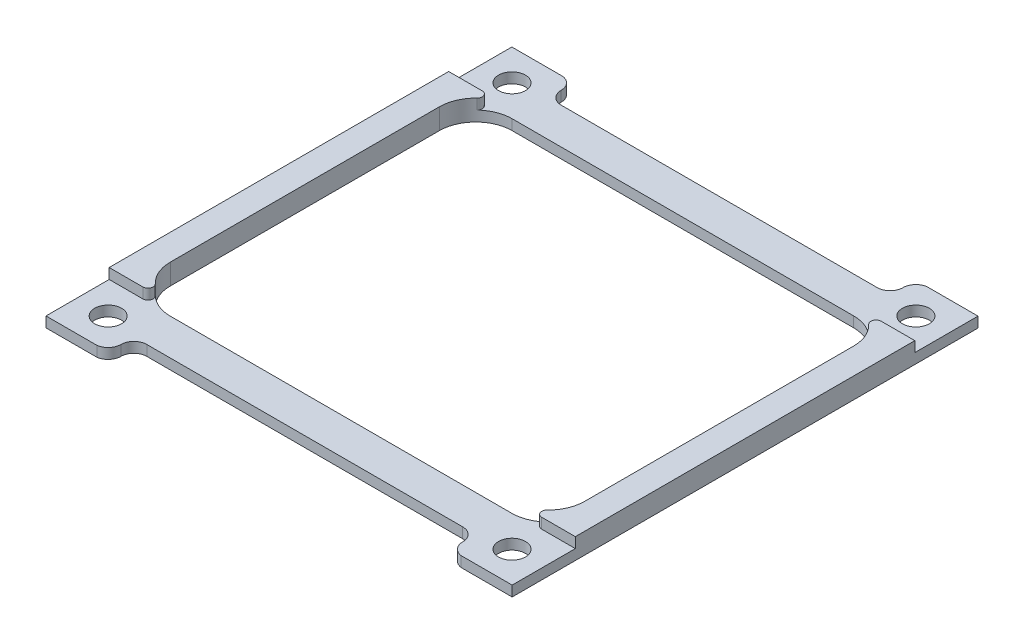
SolidWorks part; units mm, degrees
ref_plane "前视基准面" through (0, 0, 0) normal (0, 0, 1) x (1, 0, 0)
ref_plane "上视基准面" through (0, 0, 0) normal (0, 1, 0) x (1, 0, 0)
ref_plane "右视基准面" through (0, 0, 0) normal (1, 0, 0) x (0, 0, -1)
other "Configuration Table"
sketch "草图1" plane through (0, 0, 0) normal (0, 1, 0) x (1, 0, 0)
  line L1 (-39, 39) -> (39, 39) construction
  line L2 (-39, 39) -> (-39, -39) construction
  line L3 (-39, -39) -> (39, -39) construction
  line L4 (39, 39) -> (39, -39) construction
  line L9 (-45.0151, 44.9851) -> (45.0151, 44.9851)
  line L10 (-45.0151, 44.9851) -> (-45.0151, -44.9851)
  line L15 (-45.0151, -44.9851) -> (45.0151, -44.9851)
  line L16 (45.0151, 44.9851) -> (45.0151, -44.9851)
  line L17 (-32.9854, 33.0149) -> (32.9854, 33.0149)
  line L18 (-32.9854, 33.0149) -> (-32.9854, -33.0149)
  line L19 (-32.9854, -33.0149) -> (32.9854, -33.0149)
  line L20 (32.9854, 33.0149) -> (32.9854, -33.0149)
  line L21 (-32.9854, 33.0149) -> (32.9854, -33.0149) construction
  line L22 (-32.9854, -33.0149) -> (32.9854, 33.0149) construction
  circle A0 centre (39, 39) radius 2.6
  circle A1 centre (39, -39) radius 2.6
  circle A2 centre (-39, -39) radius 2.6
  circle A3 centre (-39, 39) radius 2.6
  point P0 (0, 0)
  point P10 (0, 0)
  point P11 (0, 0)
  point P15 (0, 0)
  point P16 (0, 0)
  dimension "D2" = 5.2
  dimension "D1" = 78
extrude "凸台-拉伸1" add sketch "草图1" along normal blind 2
sketch "草图3" plane through (0, 2, 0) normal (0, 1, 0) x (1, 0, 0)
  line L0 (0, 44.9851) -> (0, -44.9851) construction
  line L1 (45.0151, 44.9851) -> (-45.0151, 44.9851) construction
  line L2 (-45.0151, -44.9851) -> (45.0151, -44.9851) construction
  line L3 (45.0151, 0) -> (-45.0151, 0) construction
  line L4 (-35.851, 44.9851) -> (35.851, 44.9851)
  line L5 (-30.5025, 40.0211) -> (30.5025, 40.0211)
  line L6 (45.0151, -44.9851) -> (45.0151, 44.9851) construction
  line L7 (-45.0151, 44.9851) -> (-45.0151, -44.9851) construction
  line L8 (-30.5025, -40.0211) -> (30.5025, -40.0211)
  line L9 (-35.851, -44.9851) -> (35.851, -44.9851)
  arc A0 (-33.0087, 42.5087) -> (-35.851, 44.9851) centre (-35.5087, 42.5087) ccw
  arc A1 (-33.0087, 42.5087) -> (-30.5025, 40.0211) centre (-30.5087, 42.5211) ccw
  arc A2 (33.0087, 42.5087) -> (30.5025, 40.0211) centre (30.5087, 42.5211) cw
  arc A3 (33.0087, 42.5087) -> (35.851, 44.9851) centre (35.5087, 42.5087) cw
  arc A4 (33.0087, -42.5087) -> (35.851, -44.9851) centre (35.5087, -42.5087) ccw
  arc A5 (33.0087, -42.5087) -> (30.5025, -40.0211) centre (30.5087, -42.5211) ccw
  arc A6 (-33.0087, -42.5087) -> (-30.5025, -40.0211) centre (-30.5087, -42.5211) cw
  arc A7 (-33.0087, -42.5087) -> (-35.851, -44.9851) centre (-35.5087, -42.5087) cw
  point P17 (0, 40.0211)
  point P35 (0, -40.0211)
extrude "切除-拉伸1" cut sketch "草图3" against normal through all contours A2 A3 L4 A0 A1 L5 | A6 A7 L9 A4 A5 L8
sketch "草图4" plane through (0, 2, 0) normal (0, 1, 0) x (1, 0, 0)
  line L0 (-32.9854, 33.0149) -> (-32.9854, -33.0149)
  line L1 (45.0151, -44.9851) -> (45.0151, 44.9851) construction
  line L2 (32.9854, 33.0149) -> (-32.9854, 33.0149) construction
  line L3 (0, 33.0149) -> (0, 0) construction
  line L4 (0, 0) -> (45.0151, 0) construction
  line L5 (40.0151, 25.9852) -> (40.0151, -25.9852)
  line L7 (32.9854, 33.0149) -> (32.9854, -33.0149)
  line L8 (-40.0151, 25.9852) -> (-40.0151, -25.9852)
  arc A0 (32.9854, -33.0149) -> (40.0151, -25.9503) centre (32.9679, -25.9677) ccw
  arc A1 (32.9854, 33.0149) -> (40.0151, 25.9503) centre (32.9679, 25.9677) cw
  arc A2 (-32.9854, 33.0149) -> (-40.0151, 25.9503) centre (-32.9679, 25.9677) ccw
  arc A3 (-32.9854, -33.0149) -> (-40.0151, -25.9503) centre (-32.9679, -25.9677) cw
  point P19 (40.0151, 0)
  point P24 (-40.0151, 0)
  line M23 (32.9854, 33.0149) -> (32.9854, -33.0149)
  line M25 (-32.9854, -33.0149) -> (-32.9854, 33.0149)
  dimension "D1" = 5
extrude "切除-拉伸2" cut sketch "草图4" against normal through all contours A3 A2 L8 M25 | A1 A0 L5 M23
sketch "草图5" plane through (0, 2, 0) normal (0, 1, 0) x (1, 0, 0)
  line L0 (45.0151, 0) -> (0, 0) construction
  line L1 (-45.0151, -32.7851) -> (-34.7527, -32.7851)
  line L2 (-45.0151, 32.7851) -> (-34.7527, 32.7851)
  line L4 (-40.0151, 25.9852) -> (-40.0151, -25.9852) construction
  line L5 (-40.0151, 25.9852) -> (-40.0151, -25.9852)
  line L6 (40.0151, 25.9852) -> (40.0151, -25.9852) construction
  line L7 (40.0151, 25.9852) -> (40.0151, -25.9852)
  line L8 (-35.1663, 44.9851) -> (-45.0151, 44.9851)
  line L9 (-45.0151, 44.9851) -> (-45.0151, -44.9851)
  line L10 (-45.0151, -44.9851) -> (-35.1663, -44.9851)
  line L11 (-30.5087, -40.0211) -> (30.5087, -40.0211)
  line L12 (35.1663, -44.9851) -> (45.0151, -44.9851)
  line L13 (45.0151, -44.9851) -> (45.0151, 44.9851)
  line L14 (45.0151, 44.9851) -> (35.1663, 44.9851)
  line L15 (30.5087, 40.0211) -> (-30.5087, 40.0211)
  line L21 (45.0151, -44.9851) -> (45.0151, 44.9851)
  line L23 (45.0151, 32.7851) -> (45.0151, -32.7851)
  line L24 (34.7527, 32.7851) -> (45.0151, 32.7851)
  line L25 (34.7527, -32.7851) -> (45.0151, -32.7851)
  line L26 (-45.0151, 44.9851) -> (-45.0151, -44.9851) construction
  line L27 (-45.0151, 32.7851) -> (-45.0151, -32.7851)
  arc A0 (-40.0151, -25.9852) -> (-32.9854, -33.0149) centre (-32.9679, -25.9677) ccw construction
  arc A1 (-32.9854, 33.0149) -> (-40.0151, 25.9852) centre (-32.9679, 25.9677) ccw construction
  arc A2 (-40.0151, -25.9852) -> (-34.7527, -32.7851) centre (-32.9679, -25.9677) ccw
  arc A3 (-34.7527, 32.7851) -> (-40.0151, 25.9852) centre (-32.9679, 25.9677) ccw
  arc A4 (32.9854, -33.0149) -> (40.0151, -25.9852) centre (32.9679, -25.9677) ccw construction
  arc A5 (40.0151, 25.9852) -> (32.9854, 33.0149) centre (32.9679, 25.9677) ccw construction
  arc A6 (34.7527, -32.7851) -> (40.0151, -25.9852) centre (32.9679, -25.9677) ccw
  arc A7 (40.0151, 25.9852) -> (34.7527, 32.7851) centre (32.9679, 25.9677) ccw
  arc A8 (-33.0087, 42.5087) -> (-30.5087, 40.0211) centre (-30.5087, 42.5211) ccw
  arc A9 (-33.0087, 42.5087) -> (-35.1663, 44.9851) centre (-35.5087, 42.5087) ccw
  arc A10 (-35.1663, -44.9851) -> (-33.0087, -42.5087) centre (-35.5087, -42.5087) ccw
  arc A11 (-30.5087, -40.0211) -> (-33.0087, -42.5087) centre (-30.5087, -42.5211) ccw
  arc A12 (33.0087, -42.5087) -> (30.5087, -40.0211) centre (30.5087, -42.5211) ccw
  arc A13 (33.0087, -42.5087) -> (35.1663, -44.9851) centre (35.5087, -42.5087) ccw
  arc A14 (35.1663, 44.9851) -> (33.0087, 42.5087) centre (35.5087, 42.5087) ccw
  arc A15 (30.5087, 40.0211) -> (33.0087, 42.5087) centre (30.5087, 42.5211) ccw
  dimension "D1" = 0
extrude "凸台-拉伸2" add sketch "草图5" along normal blind 2
fillet "圆角1" radius 1 4 edges at (34.7527, 3, 32.7851) (-34.7527, 3, 32.7851) (-34.7527, 3, -32.7851) (34.7527, 3, -32.7851)
